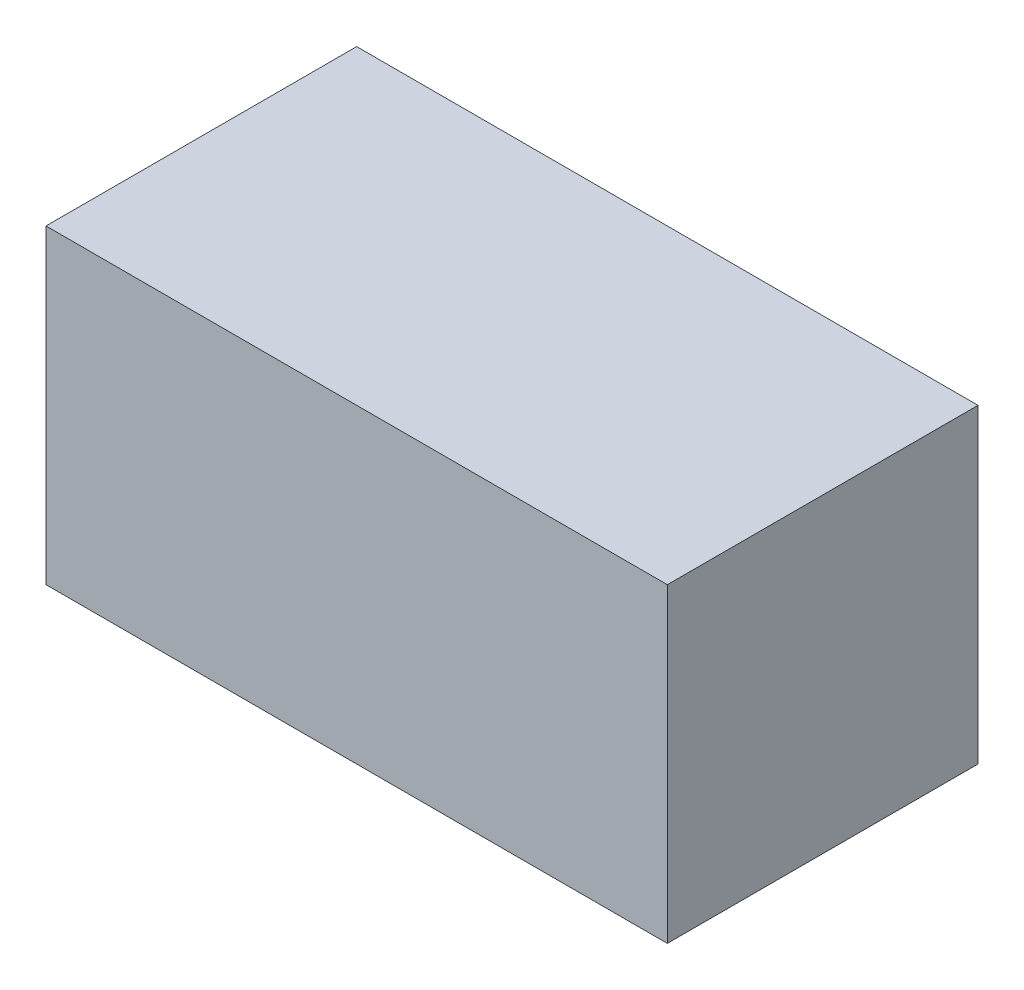
SolidWorks part; units mm, degrees
ref_plane "Front Plane" through (0, 0, 0) normal (0, 0, 1) x (1, 0, 0)
ref_plane "Top Plane" through (0, 0, 0) normal (0, 1, 0) x (1, 0, 0)
ref_plane "Right Plane" through (0, 0, 0) normal (1, 0, 0) x (0, 0, -1)
sketch "Sketch1" plane through (0, 0, 0) normal (0, 1, 0) x (1, 0, 0)
  line L0 (-10, 5) -> (10, -5) construction
  line L1 (-10, 5) -> (10, 5)
  line L2 (-10, 5) -> (-10, -5)
  line L3 (-10, -5) -> (10, -5)
  line L4 (10, 5) -> (10, -5)
  dimension "D1" = 20
  dimension "D2" = 10
extrude "Boss-Extrude1" add sketch "Sketch1" along normal blind 10
